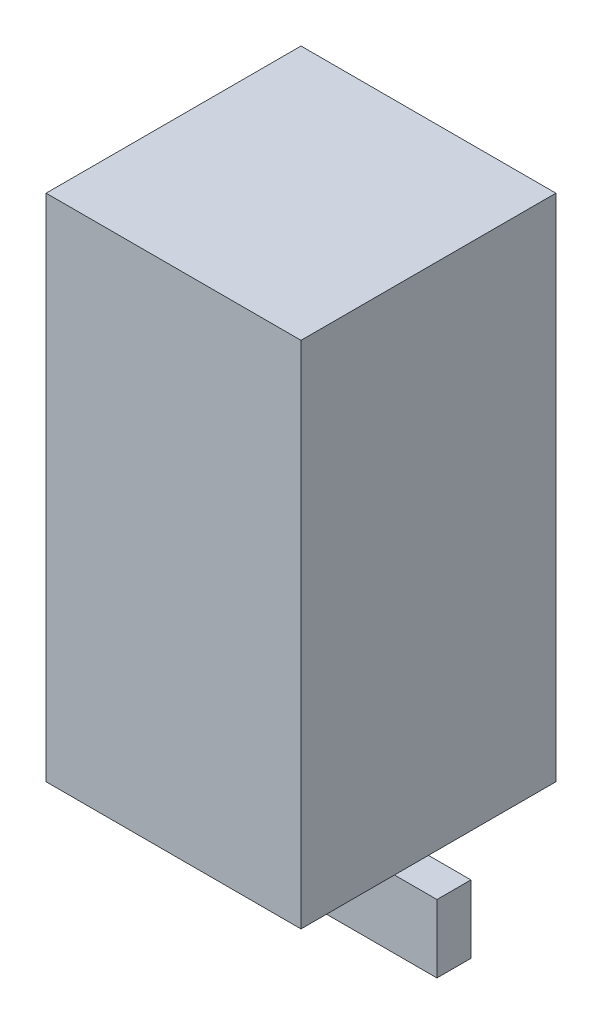
SolidWorks part; units mm, degrees
ref_plane "Front Plane" through (0, 0, 0) normal (0, 0, 1) x (1, 0, 0)
ref_plane "Top Plane" through (0, 0, 0) normal (0, 1, 0) x (1, 0, 0)
ref_plane "Right Plane" through (0, 0, 0) normal (1, 0, 0) x (0, 0, -1)
sketch "Sketch1" plane through (0, 0, 0) normal (0, 1, 0) x (1, 0, 0)
  line L1 (-15, -15) -> (15, -15)
  line L2 (-15, -15) -> (-15, 15)
  line L3 (-15, 15) -> (15, 15)
  line L4 (15, -15) -> (15, 15)
  line L5 (-15, -15) -> (15, 15) construction
  line L6 (-15, 15) -> (15, -15) construction
  point P0 (0, 0)
  dimension "D1" = 30
  dimension "D2" = 30
extrude "Boss-Extrude1" add sketch "Sketch1" along normal blind 60
sketch "Sketch2" plane through (0, 0, 0) normal (0, -1, 0) x (1, 0, 0)
  circle A0 centre (0, 0) radius 5
  dimension "D1" = 10
extrude "Boss-Extrude2" add sketch "Sketch2" along normal blind 2
sketch "Sketch4" plane through (0, 0, 0) normal (0, 0, 1) x (1, 0, 0)
  line L0 (-5, -2) -> (18, -2)
  line L2 (18, -2) -> (18, -10)
  line L3 (18, -10) -> (0.6017, -10)
  line L4 (0.6017, -10) -> (-5, -2)
  point P5 (0, 0)
  dimension "D1" = 8
  dimension "D2" = 55
  dimension "D3" = 23
extrude "Boss-Extrude3" add sketch "Sketch4" along normal blind 2 and the other way blind 2
